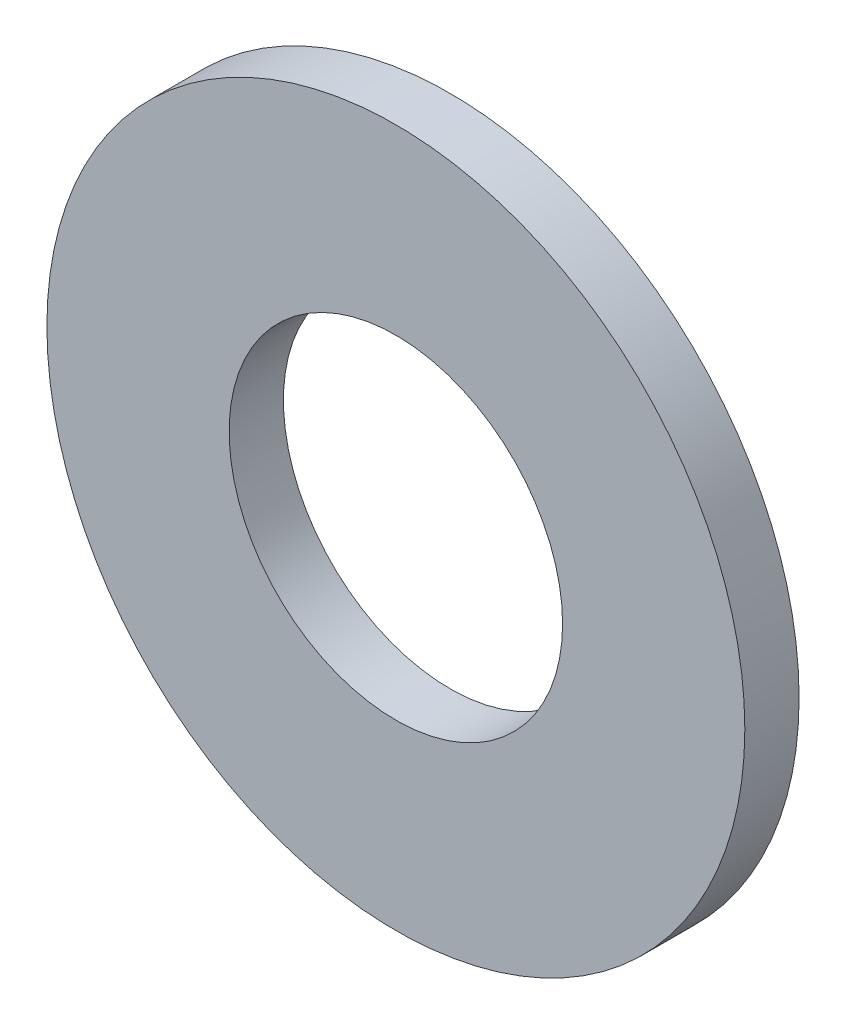
SolidWorks part; units mm, degrees
ref_plane "Front Plane" through (0, 0, 0) normal (0, 0, 1) x (1, 0, 0)
ref_plane "Top Plane" through (0, 0, 0) normal (0, 1, 0) x (1, 0, 0)
ref_plane "Right Plane" through (0, 0, 0) normal (1, 0, 0) x (0, 0, -1)
sketch "Sketch1" plane through (0, 0, 0) normal (0, 0, 1) x (1, 0, 0)
  circle A0 centre (0, 0) radius 2.15
  circle A1 centre (0, 0) radius 4.5
  dimension "ID" = 4.3
  dimension "OD" = 9
extrude "Extrude1" add sketch "Sketch1" against normal blind 0.7
